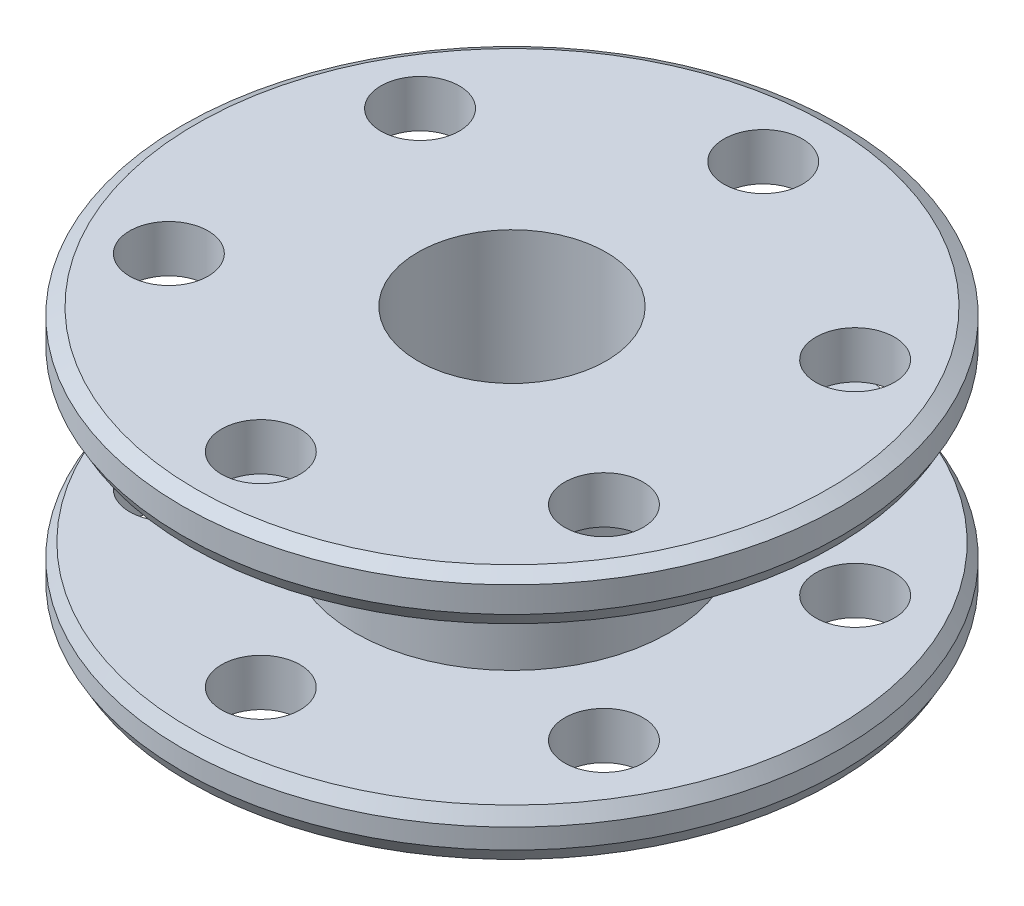
SolidWorks part; units mm, degrees
ref_plane "Front Plane" through (0, 0, 0) normal (0, 0, 1) x (1, 0, 0)
ref_plane "Top Plane" through (0, 0, 0) normal (0, 1, 0) x (1, 0, 0)
ref_plane "Right Plane" through (0, 0, 0) normal (1, 0, 0) x (0, 0, -1)
sketch "Sketch1" plane through (0, 0, 0) normal (0, 1, 0) x (1, 0, 0)
  circle A0 centre (0, 0) radius 6
  circle A1 centre (0, 0) radius 21
  circle A2 centre (0, 0) radius 16 construction
  circle A3 centre (0, 16) radius 2.5
  circle A4 centre (13.8564, 8) radius 2.5
  circle A5 centre (13.8564, -8) radius 2.5
  circle A6 centre (0, -16) radius 2.5
  circle A7 centre (-13.8564, -8) radius 2.5
  circle A8 centre (-13.8564, 8) radius 2.5
  dimension "D1" = 42
  dimension "D2" = 12
  dimension "D3" = 32
  dimension "D4" = 5
  dimension "D5" = 6
extrude "Boss-Extrude1" add sketch "Sketch1" along normal blind 16
sketch "Sketch2" plane through (0, 0, 0) normal (1, 0, 0) x (0, 0, -1)
  line L0 (0, 0) -> (0, 20.0974) construction
  line L1 (-21, 0) -> (21, 0) construction
  line L2 (21, 16) -> (-21, 16) construction
  line L3 (10, 13) -> (29.1888, 13)
  line L4 (10, 13) -> (10, 3)
  line L5 (10, 3) -> (29.1888, 3)
  line L6 (29.1888, 13) -> (29.1888, 3)
  dimension "D1" = 3
  dimension "D2" = 3
  dimension "D3" = 10
revolve "Cut-Revolve1" cut sketch "Sketch2" angle 360 about L0
chamfer "Chamfer1" distance 0.5 angle 60 4 edges at (0, 0, 21) (0, 3, -21) (0, 16, 21) (0, 13, 21)
